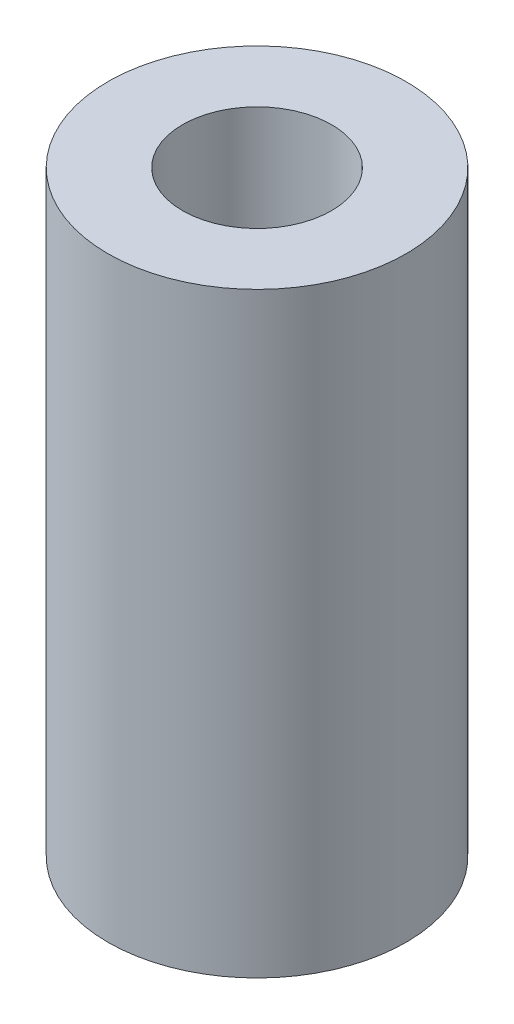
SolidWorks part; units mm, degrees
ref_plane "Front Plane" through (0, 0, 0) normal (0, 0, 1) x (1, 0, 0)
ref_plane "Top Plane" through (0, 0, 0) normal (0, 1, 0) x (1, 0, 0)
ref_plane "Right Plane" through (0, 0, 0) normal (1, 0, 0) x (0, 0, -1)
sketch "Sketch1" plane through (0, 0, 0) normal (0, 1, 0) x (1, 0, 0)
  circle A0 centre (0, 0) radius 1.5875
  circle A1 centre (0, 0) radius 3.175
  dimension "D1" = 3.175
  dimension "D2" = 6.35
extrude "Boss-Extrude1" add sketch "Sketch1" along normal blind 12.7
